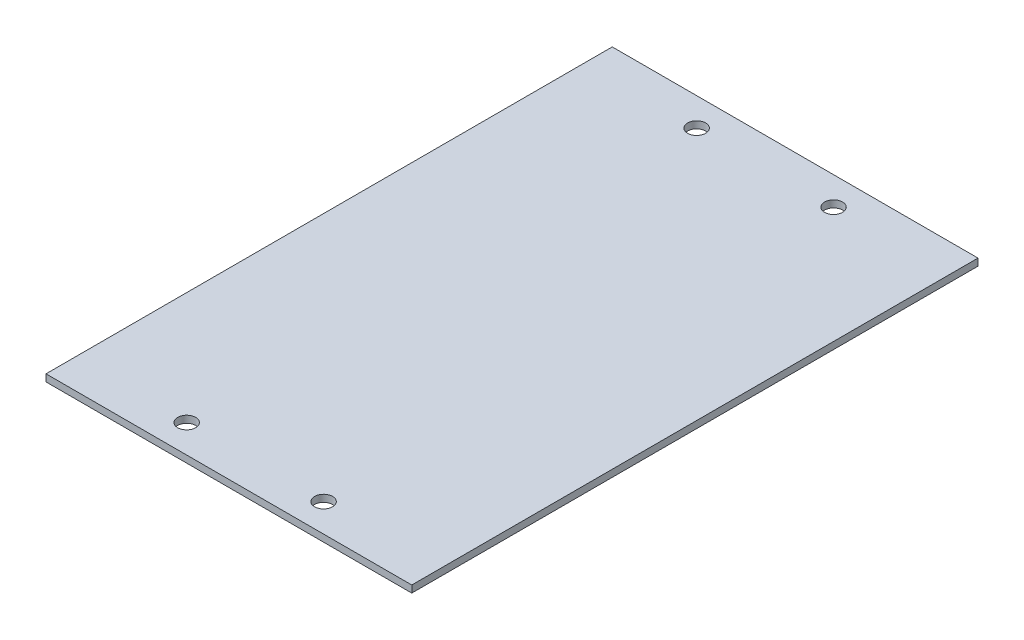
SolidWorks part; units mm, degrees
material "Balsa"
ref_plane "Front Plane" through (0, 0, 0) normal (0, 0, 1) x (1, 0, 0)
ref_plane "Top Plane" through (0, 0, 0) normal (0, 1, 0) x (1, 0, 0)
ref_plane "Right Plane" through (0, 0, 0) normal (1, 0, 0) x (0, 0, -1)
sketch "Sketch3" plane through (0, 0, 0) normal (0, 0, 1) x (1, 0, 0)
  line L1 (0, 0) -> (330.2, 0)
  line L2 (0, 0) -> (0, 6.35)
  line L3 (0, 6.35) -> (330.2, 6.35)
  line L4 (330.2, 0) -> (330.2, 6.35)
  dimension "D1" = 6.35
  dimension "D2" = 330.2
extrude "Boss-Extrude1" add sketch "Sketch3" against normal blind 511.175
sketch "Sketch4" plane through (0, 0, 0) normal (0, 1, 0) x (1, 0, 0)
  line L0 (0, 0) -> (330.2, 0) construction
  line L1 (163.3996, 0) -> (163.3996, 511.175) construction
  line L2 (330.2, 511.175) -> (0, 511.175) construction
  line L3 (163.3996, 511.175) -> (330.2, 511.175) construction
  line L4 (330.2, 511.175) -> (0, 511.175) construction
  line L5 (0, 511.175) -> (163.3996, 511.175) construction
  line L6 (0, -3.4925) -> (0, 3.4925) construction
  line L7 (163.3996, 255.5875) -> (0, 255.5875) construction
  line L8 (0, 511.175) -> (0, 0) construction
  line L9 (0, 255.5875) -> (330.2, 255.5875) construction
  line L10 (330.2, 511.175) -> (330.2, 0) construction
  circle A0 centre (101.6, 25.4) radius 8.128
  circle A1 centre (225.1991, 25.4) radius 8.128
  circle A2 centre (225.1991, 485.775) radius 8.128
  circle A3 centre (101.6, 485.775) radius 8.128
  dimension "D1" = 16.256
  dimension "D2" = 25.4
  dimension "D3" = 101.6
extrude "Cut-Extrude1" cut sketch "Sketch4" along normal through all
sketch "Sketch5" plane through (0, 6.35, 0) normal (0, 1, 0) x (1, 0, 0)
  line L0 (0, 0) -> (165.1, 0) construction
  line L1 (330.2, 0) -> (0, 0) construction
  line L2 (165.1, 0) -> (330.2, 0) construction
  line L3 (165.1, 0) -> (88.9, 0) construction
  line L4 (88.9, 0) -> (88.9, -22.0066) construction
  line L5 (88.9, -22.0066) -> (165.1, -22.0066) construction
  line L6 (165.1, -22.0066) -> (165.1, 0) construction
  line L7 (165.1, 0) -> (165.1, -22.0066) construction
  dimension "D1" = 165.1
  dimension "D2" = 76.2
